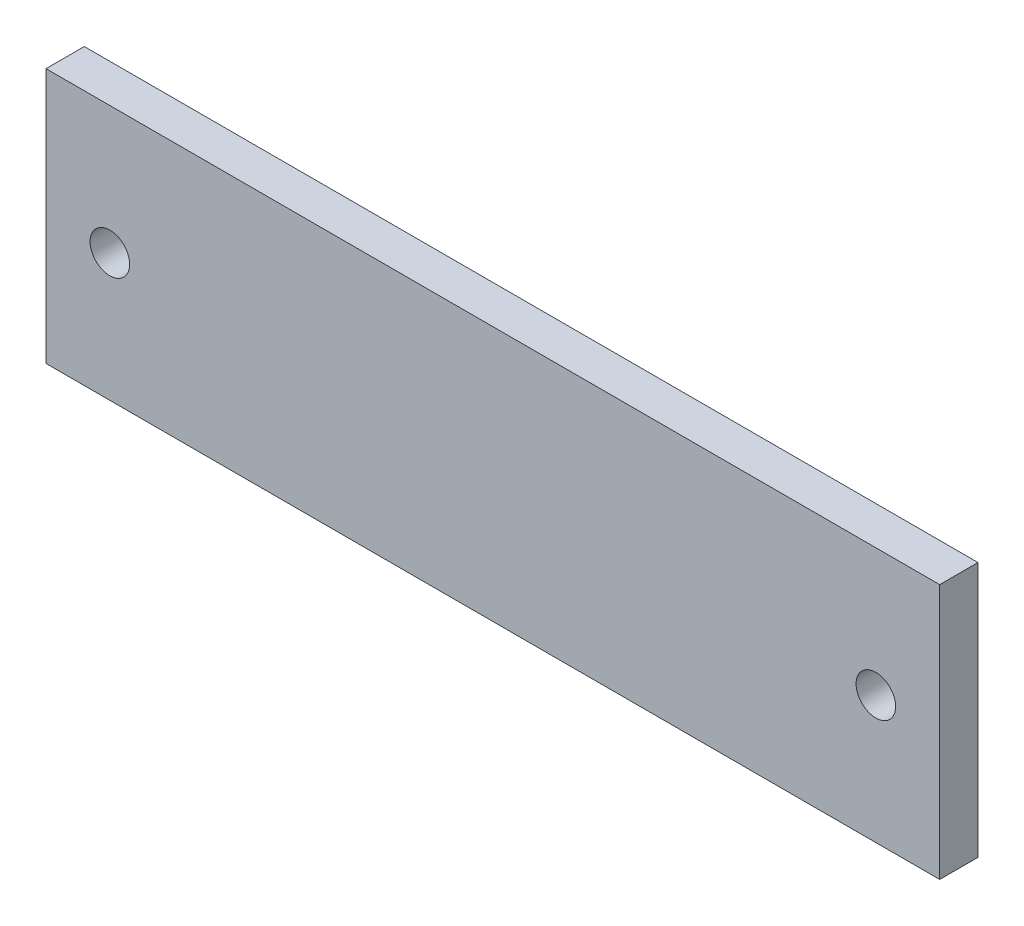
SolidWorks part; units mm, degrees
ref_plane "Front Plane" through (0, 0, 0) normal (0, 0, 1) x (1, 0, 0)
ref_plane "Top Plane" through (0, 0, 0) normal (0, 1, 0) x (1, 0, 0)
ref_plane "Right Plane" through (0, 0, 0) normal (1, 0, 0) x (0, 0, -1)
sketch "Sketch1" plane through (0, 0, 0) normal (0, 0, 1) x (1, 0, 0)
  line L0 (0, 0) -> (0, -5.7556) construction
  line L1 (-35, -10) -> (35, -10)
  line L2 (-35, -10) -> (-35, 10)
  line L3 (-35, 10) -> (35, 10)
  line L4 (35, -10) -> (35, 10)
  line L5 (-35, -10) -> (35, 10) construction
  line L6 (-35, 10) -> (35, -10) construction
  circle A0 centre (30, 0) radius 1.55
  circle A1 centre (-30, 0) radius 1.55
  point P0 (0, 0)
  dimension "D2" = 3.1
  dimension "D1" = 70
  dimension "D3" = 30
  dimension "D4" = 20
extrude "Boss-Extrude1" add sketch "Sketch1" along normal blind 3
